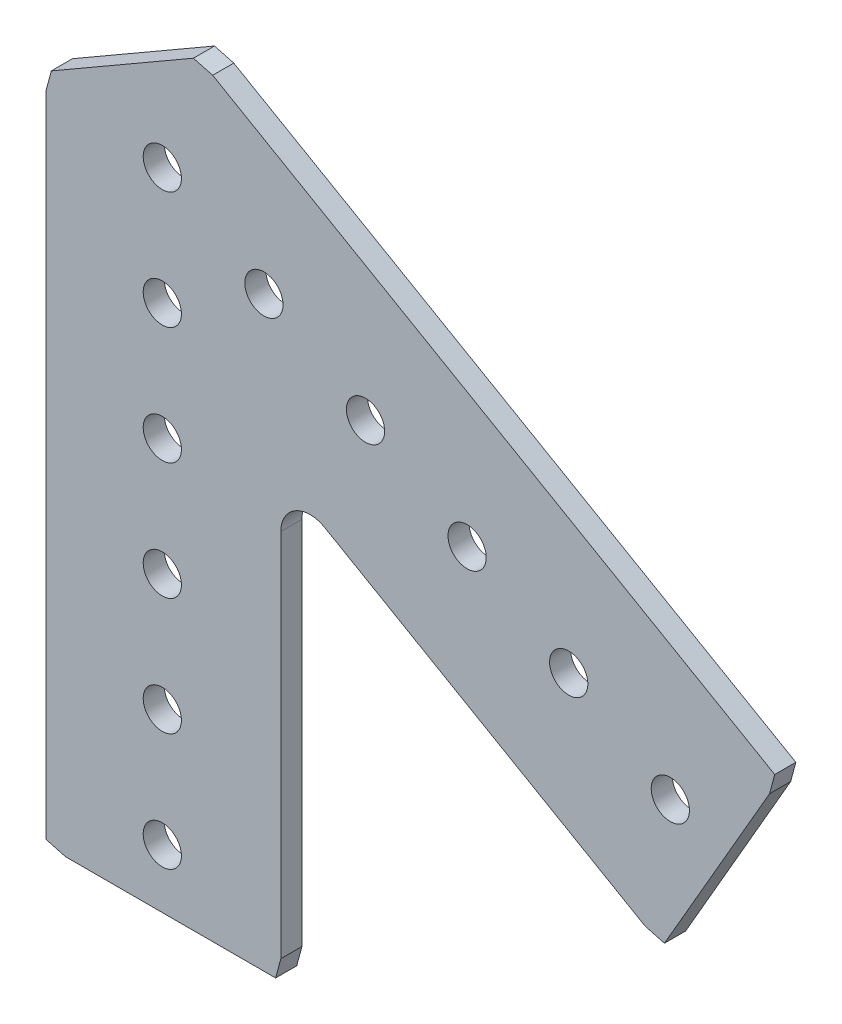
SolidWorks part; units mm, degrees
ref_plane "Front Plane" through (0, 0, 0) normal (0, 0, 1) x (1, 0, 0)
ref_plane "Top Plane" through (0, 0, 0) normal (0, 1, 0) x (1, 0, 0)
ref_plane "Right Plane" through (0, 0, 0) normal (1, 0, 0) x (0, 0, -1)
ref_plane "Plane1" through (0, 0, 2.286) normal (0, 0, 1) x (1, 0, 0)
sketch "Sketch1" plane through (0, 0, 2.286) normal (0, 0, 1) x (1, 0, 0)
  line L0 (17.5895, -24.9666) -> (52.2723, -44.9908)
  line L1 (52.2723, -44.9908) -> (54.3578, -45.5496)
  line L2 (54.3578, -45.5496) -> (65.7357, -25.8425)
  line L3 (65.7357, -25.8425) -> (66.2944, -23.7571)
  line L4 (66.2944, -23.7571) -> (5.4514, 11.3707)
  line L5 (5.4514, 11.3707) -> (3.366, 11.9295)
  line L6 (3.366, 11.9295) -> (-12.0142, 3.0497)
  line L7 (-12.0142, 3.0497) -> (-12.573, 0.9643)
  line L8 (-12.573, 0.9643) -> (-12.573, -69.2912)
  line L9 (-12.573, -69.2912) -> (-10.4876, -69.85)
  line L10 (-10.4876, -69.85) -> (12.2682, -69.85)
  line L11 (12.2682, -69.85) -> (12.827, -67.7646)
  line L12 (12.827, -67.7646) -> (12.827, -27.7163)
  arc A0 (12.827, -27.7163) -> (17.5895, -24.9666) centre (16.002, -27.7163) cw
  circle A1 centre (54.9926, -31.75) radius 2.0701
  circle A2 centre (32.9956, -19.05) radius 2.0701
  circle A3 centre (0, -50.8) radius 2.0701
  circle A4 centre (0, -25.4) radius 2.0701
  circle A5 centre (10.9985, -6.35) radius 2.0701
  circle A6 centre (0, 0) radius 2.0701
  circle A7 centre (0, -12.7) radius 2.0701
  circle A8 centre (0, -38.1) radius 2.0701
  circle A9 centre (21.997, -12.7) radius 2.0701
  circle A10 centre (43.9941, -25.4) radius 2.0701
  circle A11 centre (0, -63.5) radius 2.0701
extrude "Boss-Extrude1" add sketch "Sketch1" against normal blind 2.286
